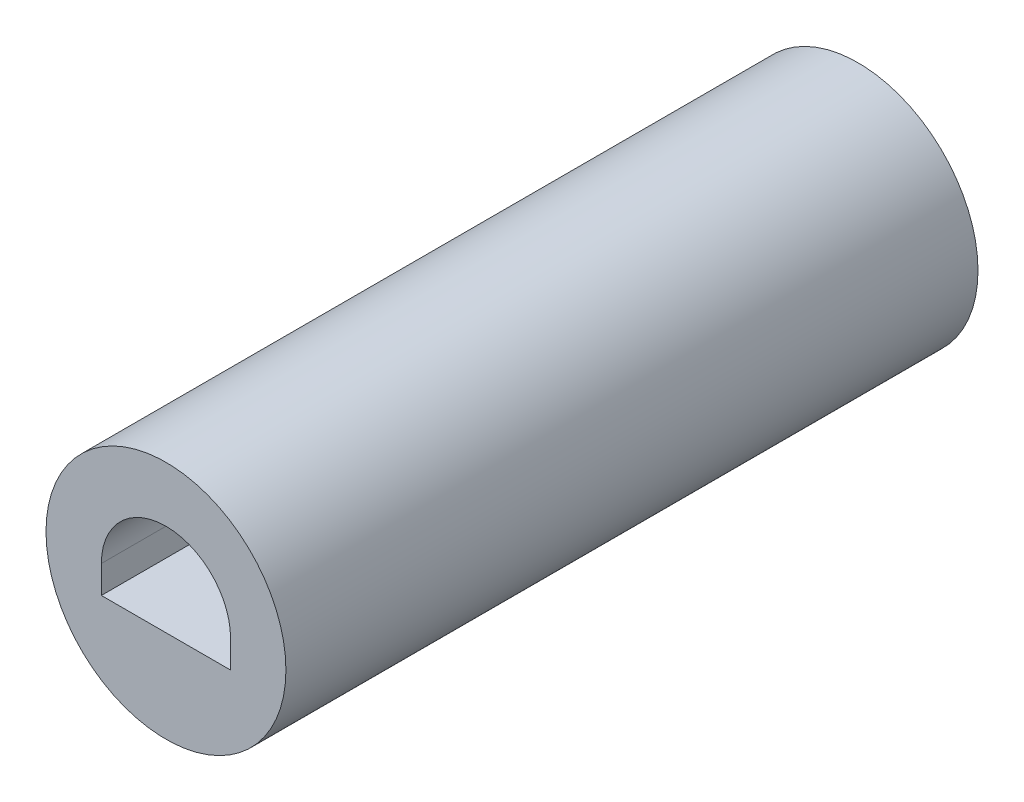
SolidWorks part; units mm, degrees
ref_plane "Front Plane" through (0, 0, 0) normal (0, 0, 1) x (1, 0, 0)
ref_plane "Top Plane" through (0, 0, 0) normal (0, 1, 0) x (1, 0, 0)
ref_plane "Right Plane" through (0, 0, 0) normal (1, 0, 0) x (0, 0, -1)
sketch "Sketch1" plane through (0, 0, 0) normal (0, 0, 1) x (1, 0, 0)
  circle A0 centre (0, 0) radius 1.651
  dimension "D1" = 3.302
extrude "Boss-Extrude1" add sketch "Sketch1" along normal blind 9.525
sketch "Sketch2" plane through (0, 0, 9.525) normal (0, 0, 1) x (1, 0, 0)
  line L0 (-0.889, 0) -> (-0.889, -0.381)
  line L1 (-0.889, -0.381) -> (0.7112, -0.381)
  line L3 (0.889, 0) -> (0.889, -0.381)
  line L4 (0.889, -0.381) -> (0.7112, -0.381)
  arc A0 (0.889, 0) -> (-0.889, 0) centre (0, 0) ccw
extrude "Cut-Extrude1" cut sketch "Sketch2" against normal blind 2.54
